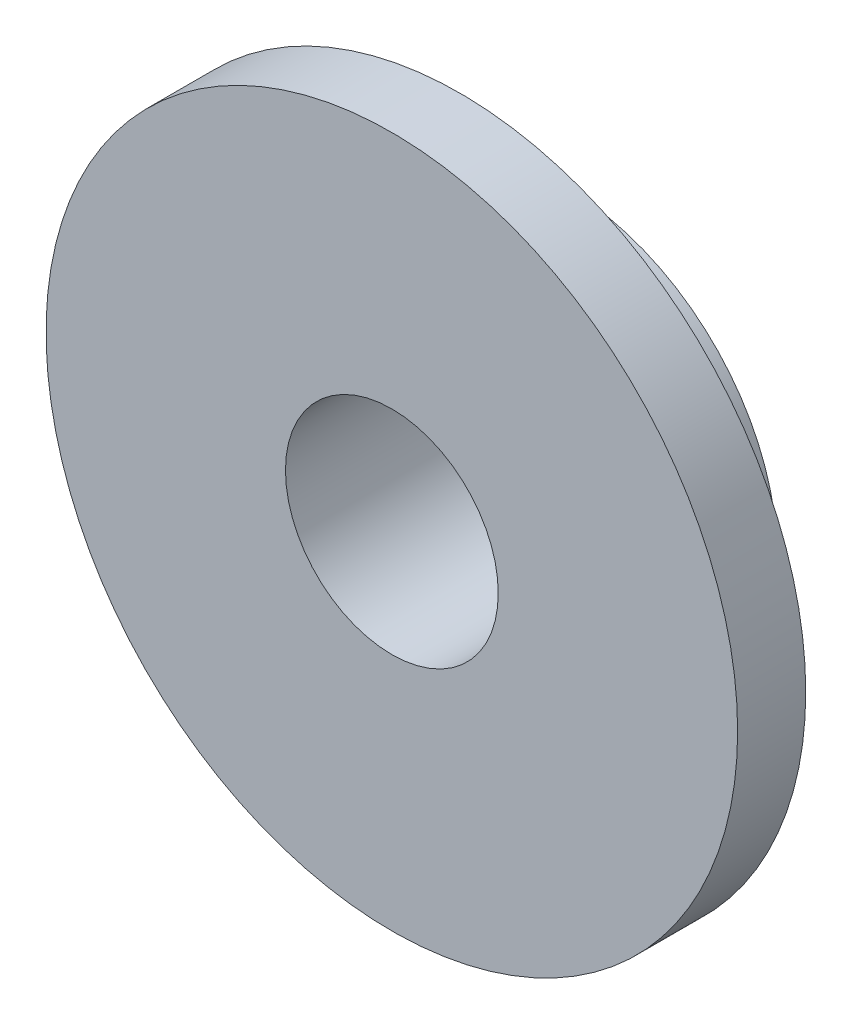
SolidWorks part; units mm, degrees
ref_plane "Front Plane" through (0, 0, 0) normal (0, 0, 1) x (1, 0, 0)
ref_plane "Top Plane" through (0, 0, 0) normal (0, 1, 0) x (1, 0, 0)
ref_plane "Right Plane" through (0, 0, 0) normal (1, 0, 0) x (0, 0, -1)
sketch "Sketch1" plane through (0, 0, 0) normal (0, 0, 1) x (1, 0, 0)
  circle A0 centre (0, 0) radius 20.6375
  circle A1 centre (0, 0) radius 6.35
extrude "Boss-Extrude1" add sketch "Sketch1" along normal blind 4.064
sketch "Sketch2" plane through (0, 0, 0) normal (0, 0, -1) x (-1, 0, 0)
  circle A0 centre (0, 0) radius 6.35
  circle A1 centre (0, 0) radius 12.7
extrude "Boss-Extrude2" add sketch "Sketch2" along normal blind 6.223
